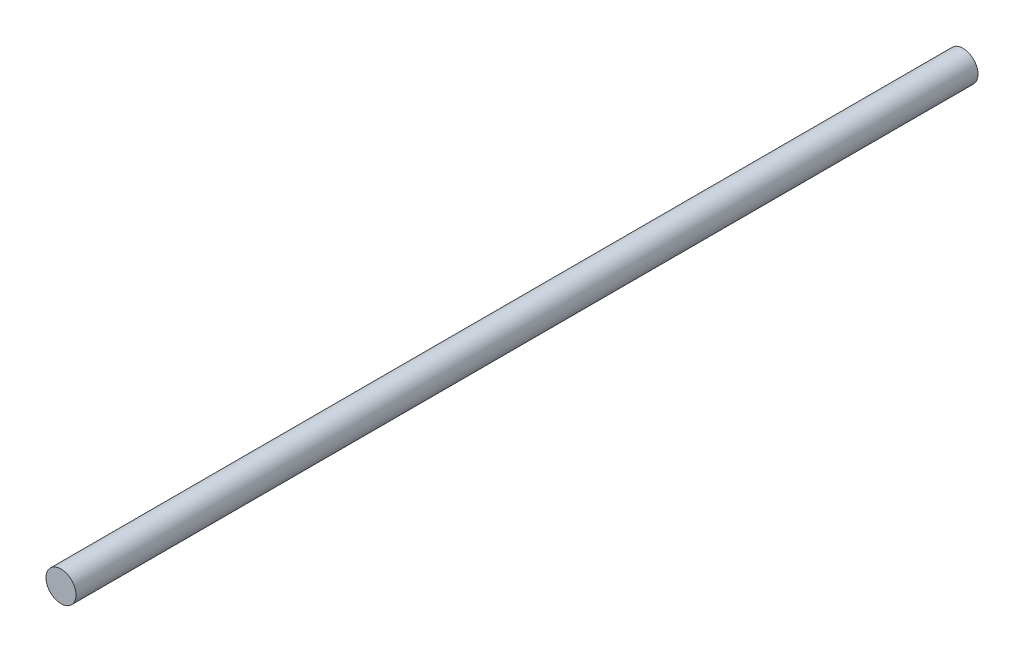
SolidWorks part; units mm, degrees
ref_plane "Front" through (0, 0, 0) normal (0, 0, 1) x (1, 0, 0)
ref_plane "Top" through (0, 0, 0) normal (0, 1, 0) x (1, 0, 0)
ref_plane "Right" through (0, 0, 0) normal (1, 0, 0) x (0, 0, -1)
sketch "草图1" plane through (0, 0, 0) normal (0, 0, 1) x (1, 0, 0)
  circle A0 centre (0, 0) radius 0.75
  dimension "D1" = 1.5
extrude "凸台-拉伸1" add sketch "草图1" along normal blind 45
